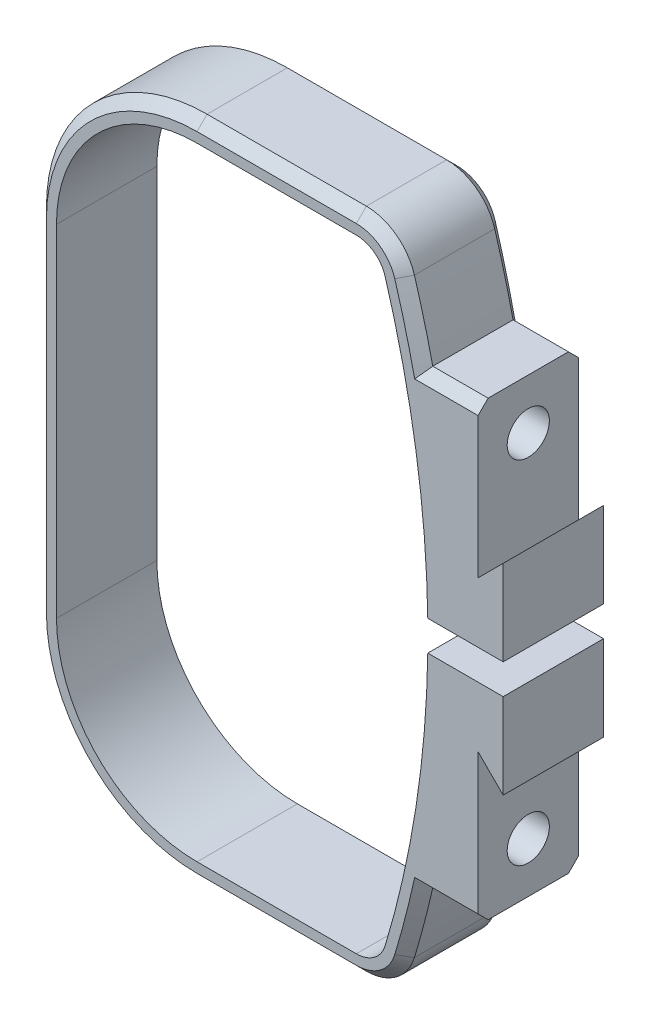
SolidWorks part; units mm, degrees
ref_plane "Alzado" through (0, 0, 0) normal (0, 0, 1) x (1, 0, 0)
ref_plane "Planta" through (0, 0, 0) normal (0, 1, 0) x (1, 0, 0)
ref_plane "Vista lateral" through (0, 0, 0) normal (1, 0, 0) x (0, 0, -1)
sketch "Croquis1" plane through (0, 0, 0) normal (0, 0, 1) x (1, 0, 0)
  line L0 (-4.5, 31) -> (11.3709, 31)
  line L1 (-18.5, 31) -> (18.5, 31) construction
  line L2 (-18.5, 31) -> (-18.5, -31) construction
  line L3 (-18.5, -31) -> (18.5, -31) construction
  line L4 (18.5, 31) -> (18.5, -31) construction
  line L5 (-18.5, 31) -> (18.5, -31) construction
  line L6 (-18.5, -31) -> (18.5, 31) construction
  line L7 (11.3709, -31) -> (-4.5, -31)
  line L8 (-18.5, -17) -> (-18.5, 17)
  line L10 (0, 0) -> (50000, 0) construction
  line L11 (-20.5, -17) -> (-20.5, 17)
  line L12 (11.3709, -33) -> (-4.5, -33)
  line L13 (-4.5, 33) -> (11.3709, 33)
  arc A0 (11.3709, 31) -> (14.2432, 28.866) centre (11.3709, 28) cw
  arc A1 (-4.5, -31) -> (-18.5, -17) centre (-4.5, -17) cw
  arc A2 (14.2432, -28.866) -> (11.3709, -31) centre (11.3709, -28) cw
  arc A3 (-4.5, 31) -> (-18.5, 17) centre (-4.5, 17) ccw
  arc A4 (14.2432, 28.866) -> (14.2432, -28.866) centre (-81.5, 0) cw
  arc A5 (-4.5, 33) -> (-20.5, 17) centre (-4.5, 17) ccw
  arc A6 (-4.5, -33) -> (-20.5, -17) centre (-4.5, -17) cw
  arc A7 (16.158, -29.4433) -> (11.3709, -33) centre (11.3709, -28) cw
  arc A8 (16.158, 29.4433) -> (16.158, -29.4433) centre (-81.5, 0) cw
  arc A9 (11.3709, 33) -> (16.158, 29.4433) centre (11.3709, 28) cw
  point P0 (0, 0)
  point P20 (0, 0)
  point P21 (0, 0)
  dimension "D3" = 3
  dimension "D4" = 3
  dimension "D5" = 14
  dimension "D6" = 14
  dimension "D7" = 100
  dimension "D1" = 37
  dimension "D2" = 62
  dimension "D8" = 2
extrude "Saliente-Extruir1" add sketch "Croquis1" along normal mid plane 10
sketch "Croquis2" plane through (0, 0, 5) normal (0, 0, 1) x (1, 0, 0)
  line L0 (0, 0) -> (50000, 0) construction
  line L1 (18.5, 0) -> (18.5, 50000) construction
  line L2 (18.5, 22.5) -> (17.9874, 22.5)
  line L3 (28.5, -22.5) -> (18.5, -22.5)
  line L4 (28.5, -22.5) -> (28.5, 22.5)
  line L5 (28.5, 22.5) -> (18.5, 22.5)
  line L6 (18.5, -22.5) -> (18.5, 22.5) construction
  line L7 (28.5, -22.5) -> (18.5, 22.5) construction
  line L8 (28.5, 22.5) -> (18.5, -22.5) construction
  line L9 (17.9874, 22.5) -> (20.5, 0)
  line L10 (20.5, 0) -> (17.9874, -22.5)
  line L11 (17.9874, -22.5) -> (18.5, -22.5)
  arc A0 (14.2432, -28.866) -> (14.2432, 28.866) centre (-81.5, 0) ccw construction
  arc A1 (16.158, -29.4433) -> (16.158, 29.4433) centre (-81.5, 0) ccw construction
  point P8 (18.5, 0)
  point P9 (23.5, 0)
  dimension "D1" = 10
  dimension "D2" = 45
extrude "Saliente-Extruir2" add sketch "Croquis2" against normal through all
sketch "Croquis3" plane through (0, 0, 5) normal (0, 0, 1) x (1, 0, 0)
  line L0 (23.5, 22.5) -> (23.5, 7.5)
  line L1 (28.5, 22.5) -> (17.9874, 22.5) construction
  line L2 (23.5, 7.5) -> (26, 10)
  line L4 (0, 0) -> (50000, 0) construction
  line L5 (21.4843, 22.5) -> (50021.4843, 22.5) construction
  line L6 (27.932, -22.5) -> (-44291.6464, -22.5) construction
  line L8 (23.5, 22.5) -> (28.5, 22.5)
  line L9 (28.5, 22.5) -> (28.5, -22.5)
  line L10 (28.5, -22.5) -> (23.5, -22.5)
  line L11 (23.5, -22.5) -> (23.5, -7.5)
  line L12 (23.5, -7.5) -> (26, -10)
  line L13 (26, -10) -> (26, 10)
  point P6 (26, 0)
  dimension "D1" = 5
  dimension "D2" = 2.5
  dimension "D3" = 20
  dimension "D4" = 45
extrude "Cortar-Extruir1" cut sketch "Croquis3" against normal through all
sketch "Croquis8" plane through (28.5, 0, 0) normal (1, 0, 0) x (0, 0, -1)
  line L0 (0, 0) -> (0, 50000) construction
  line L1 (0, 0) -> (50000, 0) construction
  circle A0 centre (0, 17.5) radius 2.1
  circle A1 centre (0, -17.5) radius 2.1
  dimension "D1" = 4.2
  dimension "D2" = 35
extrude "Cortar-Extruir5" [suppressed] cut sketch "Croquis8" against normal through all
sketch "Croquis4" plane through (0, 0, 5) normal (0, 0, 1) x (1, 0, 0)
  line L0 (0, 0) -> (50000, 0) construction
  line L1 (26, 10) -> (26, -10) construction
  line L2 (11, 1.5) -> (26, 1.5)
  line L3 (11, 1.5) -> (11, -1.5)
  line L4 (11, -1.5) -> (26, -1.5)
  line L5 (26, 1.5) -> (26, -1.5)
  line L6 (11, 1.5) -> (26, -1.5) construction
  line L7 (11, -1.5) -> (26, 1.5) construction
  arc A0 (14.2432, -28.866) -> (14.2432, 28.866) centre (-81.5, 0) ccw construction
  point P3 (18.5, 0)
  point P8 (26, 2.1301)
  point P11 (18.5, 0)
  dimension "D1" = 3
extrude "Cortar-Extruir2" cut sketch "Croquis4" against normal through all
sketch "Croquis6" plane through (23.5, 0, 0) normal (1, 0, 0) x (0, 0, -1)
  line L0 (0, 0) -> (0, -50000) construction
  line L1 (0, 0) -> (50000, 0) construction
  circle A0 centre (0, 17.5) radius 2.1
  circle A1 centre (0, -17.5) radius 2.1
  dimension "D1" = 4.2
  dimension "D2" = 35
extrude "Cortar-Extruir3" cut sketch "Croquis6" against normal up to next
sketch "Croquis7" plane through (23.5, 0, 0) normal (1, 0, 0) x (0, 0, -1)
  line L0 (0, 0) -> (50000, 0) construction
  line L1 (-3.45, 20.95) -> (3.45, 20.95)
  line L2 (-3.45, 20.95) -> (-3.45, 14.05)
  line L3 (-3.45, 14.05) -> (3.45, 14.05)
  line L4 (3.45, 20.95) -> (3.45, 14.05)
  line L5 (-3.45, 20.95) -> (3.45, 14.05) construction
  line L6 (-3.45, 14.05) -> (3.45, 20.95) construction
  line L7 (-3.45, -14.05) -> (3.45, -20.95) construction
  line L8 (-3.45, -20.95) -> (3.45, -14.05) construction
  line L9 (3.45, -20.95) -> (3.45, -14.05)
  line L10 (-3.45, -14.05) -> (3.45, -14.05)
  line L11 (-3.45, -20.95) -> (-3.45, -14.05)
  line L12 (-3.45, -20.95) -> (3.45, -20.95)
  point P0 (0, 17.5)
  point P13 (0, -17.5)
  dimension "D1" = 6.9
extrude "Cortar-Extruir4" cut sketch "Croquis7" against normal up to next from offset 3 offset against normal yes
chamfer "Chaflán1" distance 1 angle 45 22 edges at (20.7437, -22.5, 5) (20.7437, -22.5, -5) (20.7437, 22.5, -5) (20.7437, 22.5, 5) (17.1339, 25.9878, -5) (17.1339, -25.9878, -5) (14.3528, 32.0135, -5) (14.3528, -32.0135, -5) (3.4354, 33, -5) (3.4354, -33, -5) (-15.8137, 28.3137, -5) (-15.8137, -28.3137, -5) (-20.5, 0, -5) (17.1339, -25.9878, 5) (14.3528, -32.0135, 5) (17.1339, 25.9878, 5) (3.4354, -33, 5) (14.3528, 32.0135, 5) (-15.8137, -28.3137, 5) (3.4354, 33, 5) (-20.5, 0, 5) (-15.8137, 28.3137, 5)
